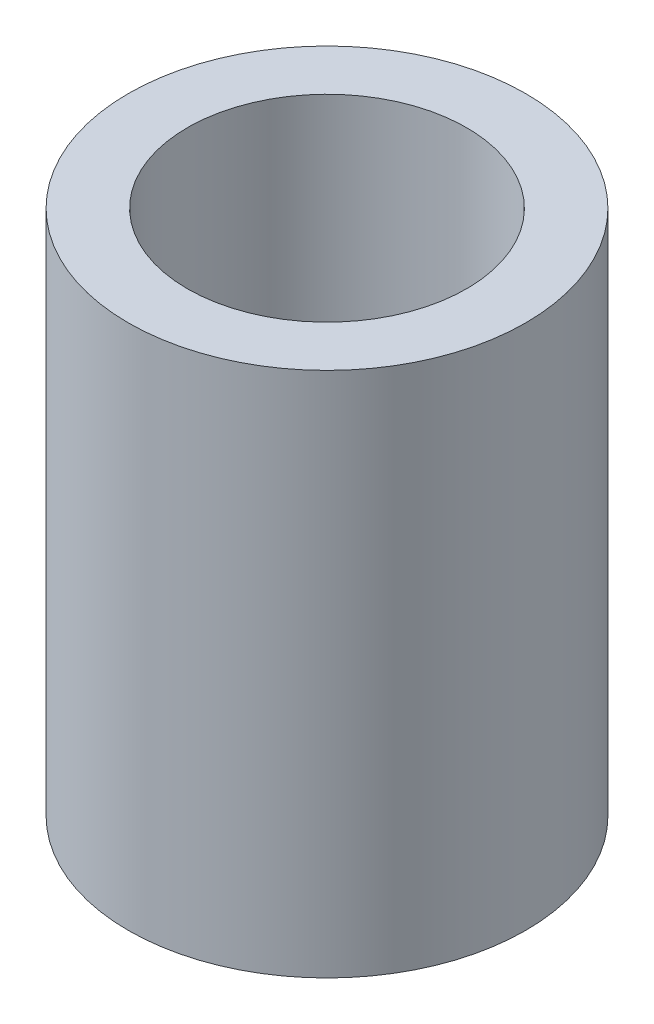
SolidWorks part; units mm, degrees
ref_plane "Front Plane" through (0, 0, 0) normal (0, 0, 1) x (1, 0, 0)
ref_plane "Top Plane" through (0, 0, 0) normal (0, 1, 0) x (1, 0, 0)
ref_plane "Right Plane" through (0, 0, 0) normal (1, 0, 0) x (0, 0, -1)
sketch "Sketch1" plane through (0, 0, 0) normal (0, 1, 0) x (1, 0, 0)
  circle A0 centre (0, 0) radius 4.699
  circle A1 centre (0, 0) radius 3.302
  dimension "D1" = 6.604
  dimension "D2" = 9.398
extrude "Boss-Extrude1" add sketch "Sketch1" along normal blind 12.446
